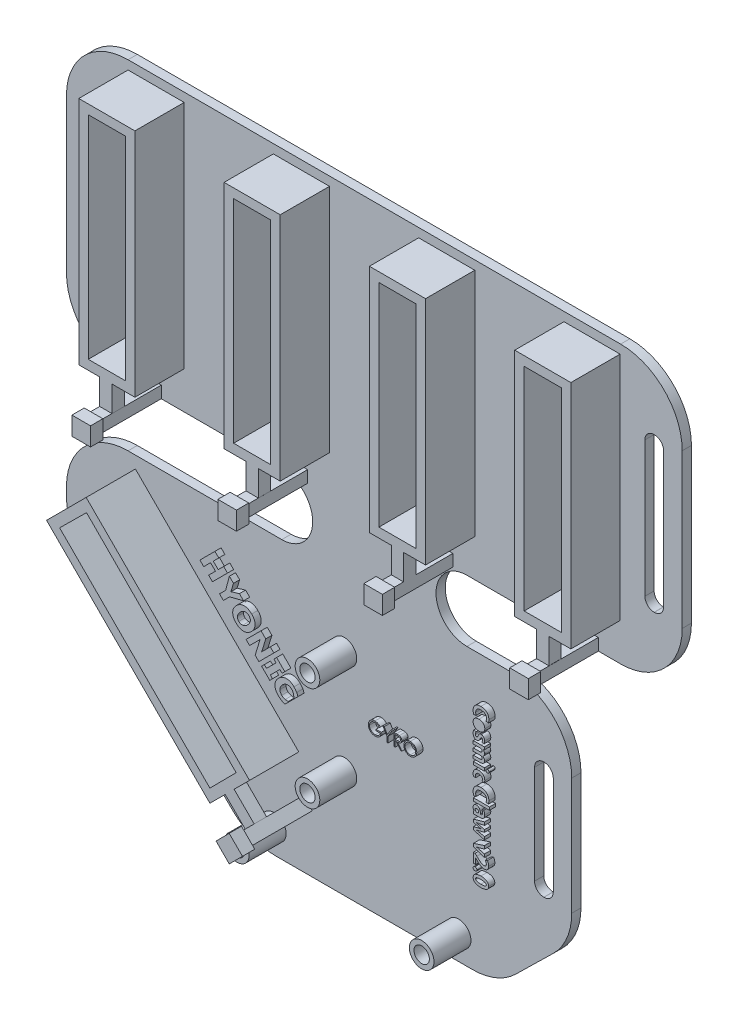
SolidWorks part; units mm, degrees
ref_plane "Front Plane" through (0, 0, 0) normal (0, 0, 1) x (1, 0, 0)
ref_plane "Top Plane" through (0, 0, 0) normal (0, 1, 0) x (1, 0, 0)
ref_plane "Right Plane" through (0, 0, 0) normal (1, 0, 0) x (0, 0, -1)
sketch "Sketch2" plane through (0, 0, 0) normal (0, 0, 1) x (1, 0, 0)
  line L1 (-56.1458, 50) -> (23.8542, 50)
  line L2 (-66.1458, 40) -> (-66.1458, 15.009)
  line L3 (-32.1008, -50) -> (-0.1909, -50)
  line L4 (33.8542, 40) -> (33.8542, 15.009)
  line L5 (-31.1727, 5.009) -> (-66.1458, 5.009) construction
  line L7 (-66.1458, -5.009) -> (-31.1727, -5.009) construction
  line L9 (33.8542, 5.009) -> (-1.119, 5.009) construction
  line L10 (-66.1458, -15.009) -> (-66.1458, -16.4538)
  line L11 (-56.1458, 5.009) -> (-31.1727, 5.009)
  line L13 (-56.1458, -5.009) -> (-31.1727, -5.009)
  line L15 (23.8542, 5.009) -> (-1.119, 5.009)
  line L17 (5.9119, -5.009) -> (-1.119, -5.009)
  line L19 (15.9119, -15.009) -> (15.9119, -34.0239)
  line L20 (-1.119, -5.009) -> (15.9119, -5.009) construction
  line L22 (-16.1458, -50) -> (3.89, -50) construction
  line L23 (-16.1458, -50) -> (-36.1817, -50) construction
  line L24 (-63.1424, -23.5986) -> (-39.0974, -47.1448)
  line L27 (6.8057, -47.1448) -> (12.9084, -41.1687)
  arc A0 (-31.1727, -5.009) -> (-31.1727, 5.009) centre (-31.1727, 0) ccw
  arc A1 (-1.119, 5.009) -> (-1.119, -5.009) centre (-1.119, 0) ccw
  arc A2 (-32.1008, -50) -> (-39.0974, -47.1448) centre (-32.1008, -40) cw
  arc A3 (6.8057, -47.1448) -> (-0.1909, -50) centre (-0.1909, -40) cw
  arc A6 (-66.1458, -15.009) -> (-56.1458, -5.009) centre (-56.1458, -15.009) cw
  arc A7 (-66.1458, -16.4538) -> (-63.1424, -23.5986) centre (-56.1458, -16.4538) ccw
  arc A8 (-56.1458, 5.009) -> (-66.1458, 15.009) centre (-56.1458, 15.009) cw
  arc A9 (23.8542, 50) -> (33.8542, 40) centre (23.8542, 40) cw
  arc A10 (-56.1458, 50) -> (-66.1458, 40) centre (-56.1458, 40) ccw
  arc A11 (23.8542, 5.009) -> (33.8542, 15.009) centre (23.8542, 15.009) ccw
  arc A12 (12.9084, -41.1687) -> (15.9119, -34.0239) centre (5.9119, -34.0239) ccw
  arc A13 (5.9119, -5.009) -> (15.9119, -15.009) centre (5.9119, -15.009) cw
  point P17 (0, 0)
  point P39 (33.8542, 50)
  point P42 (-66.1458, 50)
  dimension "D2" = 10
  dimension "D3" = 10
  dimension "D4" = 10
  dimension "D1" = 100
extrude "Boss-Extrude2" add sketch "Sketch2" against normal blind 1.5 contours A7 L10 A6 L13 A0 L11 A8 L2 A10 L1 A9 L4 A11 L15 A1 L17 A13 L19 A12 L27 A3 L3 A2 L24
sketch "Sketch3" plane through (0, 0, 0) normal (0, 0, 1) x (1, 0, 0)
  circle A0 centre (-21.0035, -15.6832) radius 2
  circle A1 centre (-21.0035, -32.5746) radius 2
  dimension "D1" = 4
  dimension "D2" = 4
extrude "Boss-Extrude7" add sketch "Sketch3" along normal blind 6
sketch "Sketch8" plane through (0, 0, 6) normal (0, 0, 1) x (1, 0, 0)
  circle A0 centre (-21.0035, -15.6832) radius 1.25
  circle A1 centre (-21.0035, -32.5746) radius 1.25
  dimension "D1" = 2.5
  dimension "D2" = 2.5
extrude "Cut-Extrude1" cut sketch "Sketch8" against normal blind 5
sketch "Sketch9" plane through (0, 0, 0) normal (0, 0, 1) x (1, 0, 0)
  line L0 (-32.4619, -46.0299) -> (-2.4559, -46.0299) construction
  circle A0 centre (-32.4619, -46.0299) radius 2
  circle A1 centre (-2.4559, -46.0299) radius 2
  dimension "D1" = 4
  dimension "D2" = 4
extrude "Boss-Extrude8" add sketch "Sketch9" along normal blind 6
sketch "Sketch10" plane through (0, 0, 6) normal (0, 0, 1) x (1, 0, 0)
  circle A0 centre (-32.4619, -46.0299) radius 1.25
  circle A1 centre (-2.4559, -46.0299) radius 1.25
  dimension "D1" = 2.5
  dimension "D2" = 2.5
extrude "Cut-Extrude2" cut sketch "Sketch10" against normal blind 5
sketch "Sketch11" plane through (0, 0, 0) normal (0, 0, 1) x (1, 0, 0)
  line L0 (-66.1458, 40) -> (-63.1043, 40) construction
  line L1 (-66.1458, 15.009) -> (-63.1043, 15.009) construction
  line L2 (-63.1424, -23.5986) -> (-61.0425, -21.4987) construction
  line L3 (-61.6043, 40) -> (-61.5553, 40)
  line L4 (-63.1043, 38.5) -> (-63.1043, 16.509)
  line L5 (-61.6043, 15.009) -> (-61.5553, 15.009)
  line L6 (-60.0553, 38.5) -> (-60.0553, 16.509)
  line L7 (-61.0425, -21.4987) -> (-43.3557, -39.1855) construction
  line L8 (-43.3557, -39.1855) -> (-45.4556, -41.2854) construction
  line L9 (-59.9818, -22.5594) -> (-44.4164, -38.1248)
  line L10 (-42.295, -38.1248) -> (-42.2889, -38.1187)
  line L11 (-42.2889, -35.9973) -> (-57.8543, -20.4319)
  line L12 (-59.9757, -20.4319) -> (-59.9818, -20.438)
  line L13 (15.9119, -15.009) -> (12.9157, -15.009) construction
  line L14 (12.9157, -15.009) -> (12.9157, -34.0239) construction
  line L15 (12.9157, -34.0239) -> (15.9119, -34.0239) construction
  line L16 (33.8542, 40) -> (30.8329, 40) construction
  line L17 (30.8329, 40) -> (30.8329, 15.009) construction
  line L18 (30.8329, 15.009) -> (33.8542, 15.009) construction
  line L20 (29.3329, 40) -> (29.2903, 40)
  line L21 (30.8329, 38.5) -> (30.8329, 16.509)
  line L22 (29.3329, 15.009) -> (29.2903, 15.009)
  line L23 (27.7903, 38.5) -> (27.7903, 16.509)
  line L24 (11.4157, -15.009) -> (11.3731, -15.009)
  line L25 (12.9157, -16.509) -> (12.9157, -32.5239)
  line L26 (11.4157, -34.0239) -> (11.3731, -34.0239)
  line L27 (9.8731, -16.509) -> (9.8731, -32.5239)
  arc A0 (29.2903, 40) -> (27.7903, 38.5) centre (29.2903, 38.5) ccw
  arc A1 (29.3329, 40) -> (30.8329, 38.5) centre (29.3329, 38.5) cw
  arc A2 (30.8329, 16.509) -> (29.3329, 15.009) centre (29.3329, 16.509) cw
  arc A3 (29.2903, 15.009) -> (27.7903, 16.509) centre (29.2903, 16.509) cw
  arc A4 (11.4157, -15.009) -> (12.9157, -16.509) centre (11.4157, -16.509) cw
  arc A5 (11.3731, -15.009) -> (9.8731, -16.509) centre (11.3731, -16.509) ccw
  arc A6 (12.9157, -32.5239) -> (11.4157, -34.0239) centre (11.4157, -32.5239) cw
  arc A7 (11.3731, -34.0239) -> (9.8731, -32.5239) centre (11.3731, -32.5239) cw
  arc A8 (-42.2889, -38.1187) -> (-42.2889, -35.9973) centre (-43.3495, -37.058) ccw
  arc A9 (-44.4164, -38.1248) -> (-42.295, -38.1248) centre (-43.3557, -37.0642) ccw
  arc A10 (-59.9818, -22.5594) -> (-59.9818, -20.438) centre (-58.9212, -21.4987) cw
  arc A11 (-57.8543, -20.4319) -> (-59.9757, -20.4319) centre (-58.915, -21.4925) ccw
  arc A12 (-61.5553, 15.009) -> (-60.0553, 16.509) centre (-61.5553, 16.509) ccw
  arc A13 (-61.6043, 15.009) -> (-63.1043, 16.509) centre (-61.6043, 16.509) cw
  arc A14 (-61.5553, 40) -> (-60.0553, 38.5) centre (-61.5553, 38.5) cw
  arc A15 (-63.1043, 38.5) -> (-61.6043, 40) centre (-61.6043, 38.5) cw
  dimension "D1" = 1.5
extrude "Cut-Extrude3" cut sketch "Sketch11" against normal up to surface (1.5 mm away) up to face at (-19.1362, -5.3071, -1.5)
sketch "Sketch12" plane through (0, 0, 0) normal (0, 0, 1) x (1, 0, 0)
  line L0 (-60.0553, 30.6424) -> (-56.1227, 30.6424) construction
  line L1 (-56.1458, 50) -> (-56.1458, 48.5494) construction
  line L2 (-32.5458, 48.5494) -> (-32.5458, 11.0834)
  line L3 (-56.1458, 48.5494) -> (-47.0304, 48.5494)
  line L4 (-56.1458, 48.5494) -> (-56.1458, 11.0834)
  line L5 (-56.1458, 11.0834) -> (-47.0304, 11.0834)
  line L6 (-47.0304, 48.5494) -> (-47.0304, 11.0834)
  line L7 (-32.5458, 48.5494) -> (-23.4304, 48.5494)
  line L8 (-23.4304, 48.5494) -> (-23.4304, 11.0834)
  line L9 (-32.5458, 11.0834) -> (-23.4304, 11.0834)
  line L10 (-8.9458, 48.5494) -> (-8.9458, 11.0834)
  line L11 (-8.9458, 48.5494) -> (0.1696, 48.5494)
  line L12 (0.1696, 48.5494) -> (0.1696, 11.0834)
  line L13 (-8.9458, 11.0834) -> (0.1696, 11.0834)
  line L14 (14.6542, 48.5494) -> (14.6542, 11.0834)
  line L15 (14.6542, 48.5494) -> (23.7696, 48.5494)
  line L16 (23.7696, 48.5494) -> (23.7696, 11.0834)
  line L17 (14.6542, 11.0834) -> (23.7696, 11.0834)
  line L18 (-56.1458, 48.5494) -> (-32.5458, 48.5494) construction
  line L19 (-61.3798, -13.3978) -> (-34.8496, -39.928)
  line L20 (-34.8496, -39.928) -> (-28.4161, -33.4944)
  line L21 (-28.4161, -33.4944) -> (-54.9463, -6.9642)
  line L22 (-54.9463, -6.9642) -> (-61.3798, -13.3978)
  dimension "D2" = 23.6
  dimension "D1" = 4
extrude "Boss-Extrude9" add sketch "Sketch12" along normal blind 8
sketch "Sketch13" plane through (0, 0, 8) normal (0, 0, 1) x (1, 0, 0)
  line L0 (-54.1669, 48.5494) -> (-54.1669, 47.0408) construction
  line L1 (-56.1458, 47.0408) -> (-54.6076, 47.0408) construction
  line L2 (-54.6076, 47.0408) -> (-54.6076, 48.5494) construction
  line L3 (-47.0304, 11.0834) -> (-47.0304, 12.632) construction
  line L4 (-47.0304, 12.632) -> (-48.5675, 12.632) construction
  line L5 (-48.5675, 12.632) -> (-48.5675, 11.0834) construction
  line L6 (-32.5458, 48.5494) -> (-30.9967, 48.5494) construction
  line L7 (-54.6076, 47.0408) -> (-48.5675, 47.0408)
  line L8 (-54.6076, 47.0408) -> (-54.6076, 12.632)
  line L9 (-54.6076, 12.632) -> (-48.5675, 12.632)
  line L10 (-48.5675, 47.0408) -> (-48.5675, 12.632)
  line L11 (-30.9967, 48.5494) -> (-30.9967, 47.0408) construction
  line L12 (-30.9967, 47.0408) -> (-32.5458, 47.0408) construction
  line L13 (-23.4304, 11.0834) -> (-23.4304, 12.632) construction
  line L14 (-23.4304, 12.632) -> (-24.9724, 12.632) construction
  line L15 (-24.9724, 12.632) -> (-24.9724, 11.0834) construction
  line L16 (-8.9458, 11.0834) -> (-8.9458, 12.632) construction
  line L17 (-8.9458, 12.632) -> (-7.4016, 12.632) construction
  line L18 (-7.4016, 12.632) -> (-7.4016, 11.0834) construction
  line L19 (-7.4016, 11.0834) -> (0.1696, 11.0834) construction
  line L20 (0.1696, 11.0834) -> (0.1696, 12.632) construction
  line L21 (0.1696, 12.632) -> (-1.3773, 12.632) construction
  line L22 (-1.3773, 12.632) -> (-1.3773, 11.0834) construction
  line L23 (-8.9458, 48.5494) -> (-7.4016, 48.5494) construction
  line L24 (-7.4016, 48.5494) -> (-7.4016, 47.0408) construction
  line L25 (-7.4016, 47.0408) -> (-8.9458, 47.0408) construction
  line L26 (14.6542, 48.5494) -> (16.1861, 48.5494) construction
  line L27 (16.1861, 48.5494) -> (16.1861, 47.0408) construction
  line L28 (16.1861, 47.0408) -> (14.6542, 47.0408) construction
  line L29 (23.7696, 11.0834) -> (23.7696, 12.632) construction
  line L30 (23.7696, 12.632) -> (22.2818, 12.632) construction
  line L31 (22.2818, 12.632) -> (22.2818, 11.0834) construction
  line L32 (-61.3798, -13.3978) -> (-60.3186, -12.3365) construction
  line L33 (-30.9967, 47.0408) -> (-24.9724, 47.0408)
  line L34 (-30.9967, 47.0408) -> (-30.9967, 12.632)
  line L35 (-30.9967, 12.632) -> (-24.9724, 12.632)
  line L36 (-24.9724, 47.0408) -> (-24.9724, 12.632)
  line L37 (-1.3773, 12.632) -> (-7.4016, 12.632)
  line L38 (-1.3773, 12.632) -> (-1.3773, 47.0408)
  line L39 (-1.3773, 47.0408) -> (-7.4016, 47.0408)
  line L40 (-7.4016, 12.632) -> (-7.4016, 47.0408)
  line L41 (16.1861, 47.0408) -> (22.2818, 47.0408)
  line L42 (16.1861, 47.0408) -> (16.1861, 12.632)
  line L43 (16.1861, 12.632) -> (22.2818, 12.632)
  line L44 (22.2818, 47.0408) -> (22.2818, 12.632)
  line L45 (-54.9463, -6.9642) -> (-61.3798, -13.3978) construction
  line L46 (-60.3186, -12.3365) -> (-59.2574, -13.3978) construction
  line L47 (-59.2574, -13.3978) -> (-60.3186, -14.459) construction
  line L48 (-61.3798, -13.3978) -> (-34.8496, -39.928) construction
  line L49 (-60.3186, -14.459) -> (-34.8496, -39.928) construction
  line L50 (-34.8496, -39.928) -> (-28.4161, -33.4944) construction
  line L51 (-28.4161, -33.4944) -> (-29.5014, -32.4091) construction
  line L52 (-28.4161, -33.4944) -> (-54.9463, -6.9642) construction
  line L53 (-29.5014, -32.4091) -> (-30.5893, -33.497) construction
  line L54 (-30.5893, -33.497) -> (-29.5039, -34.5823) construction
  line L55 (-54.9463, -6.9642) -> (-55.9749, -7.9928) construction
  line L56 (-55.9749, -7.9928) -> (-54.8908, -9.0769) construction
  line L57 (-54.8908, -9.0769) -> (-53.8622, -8.0483) construction
  line L58 (-34.8496, -39.928) -> (-35.9138, -38.8638) construction
  line L59 (-35.9138, -38.8638) -> (-34.8496, -37.7996) construction
  line L60 (-34.8496, -37.7996) -> (-33.7854, -38.8638) construction
  line L61 (-30.5893, -33.497) -> (-34.8496, -37.7996)
  line L62 (-34.8496, -37.7996) -> (-59.2574, -13.3978)
  line L63 (-59.2574, -13.3978) -> (-54.8908, -9.0769)
  line L64 (-54.8908, -9.0769) -> (-30.5893, -33.497)
extrude "Cut-Extrude4" cut sketch "Sketch13" against normal blind 7
sketch "Sketch14" plane through (0, 0, 0) normal (0, 0, 1) x (1, 0, 0)
  line L0 (-56.1458, 11.0834) -> (-47.0304, 5.009) construction
  line L1 (-56.1458, 5.009) -> (-31.1727, 5.009) construction
  line L2 (-47.0304, 5.009) -> (-47.0304, 11.0834) construction
  line L3 (-47.0304, 11.0834) -> (-56.1458, 5.009) construction
  line L4 (-50.4257, 6.9592) -> (-27.9881, 6.9303) construction
  line L13 (-28.9979, 6.9303) -> (-26.9783, 5.009) construction
  line L14 (-28.9979, 5.009) -> (-26.9783, 6.9303) construction
  line L15 (23.8542, 5.009) -> (-1.119, 5.009) construction
  line L16 (-52.7505, 6.9303) -> (-50.7505, 6.9303)
  line L17 (-52.7505, 6.9303) -> (-52.7505, 5.009)
  line L18 (-52.7505, 5.009) -> (-50.7505, 5.009)
  line L19 (-50.7505, 6.9303) -> (-50.7505, 5.009)
  line L20 (-52.7505, 6.9303) -> (-50.7505, 5.009) construction
  line L21 (-52.7505, 5.009) -> (-50.7505, 6.9303) construction
  line L22 (-28.9979, 6.9303) -> (-26.9783, 6.9303)
  line L23 (-28.9979, 6.9303) -> (-28.9979, 5.009)
  line L24 (-28.9979, 5.009) -> (-26.9783, 5.009)
  line L25 (-26.9783, 6.9303) -> (-26.9783, 5.009)
  line L26 (-28.9979, 6.9303) -> (-26.9783, 5.009) construction
  line L27 (-28.9979, 5.009) -> (-26.9783, 6.9303) construction
  line L28 (-5.3797, 6.9303) -> (-3.3965, 6.9303)
  line L29 (-5.3797, 6.9303) -> (-5.3797, 5.009)
  line L30 (-5.3797, 5.009) -> (-3.3965, 5.009)
  line L31 (-3.3965, 6.9303) -> (-3.3965, 5.009)
  line L32 (-5.3797, 6.9303) -> (-3.3965, 5.009) construction
  line L33 (-5.3797, 5.009) -> (-3.3965, 6.9303) construction
  line L34 (18.1897, 6.9303) -> (20.2341, 6.9303)
  line L35 (18.1897, 6.9303) -> (18.1897, 5.009)
  line L36 (18.1897, 5.009) -> (20.2341, 5.009)
  line L37 (20.2341, 6.9303) -> (20.2341, 5.009)
  line L38 (18.1897, 6.9303) -> (20.2341, 5.009) construction
  line L39 (18.1897, 5.009) -> (20.2341, 6.9303) construction
  point P5 (-51.7505, 5.9696)
  point P13 (-27.9881, 5.9696)
  point P21 (-27.9881, 5.9696)
  point P22 (-4.3881, 5.9696)
  point P27 (19.2119, 5.9696)
  dimension "D1" = 1.9214
  dimension "D2" = 2
extrude "Boss-Extrude10" add sketch "Sketch14" along normal blind 12
sketch "Sketch16" plane through (0, 6.9303, 0) normal (0, 1, 0) x (1, 0, 0)
  line L0 (23.7696, -8) -> (14.6542, -8) construction
  line L1 (18.1897, -8) -> (20.209, -8)
  line L2 (18.1897, -8) -> (18.1897, -6)
  line L3 (18.1897, -6) -> (20.209, -6)
  line L4 (20.209, -8) -> (20.209, -6)
  line L5 (18.1897, -12) -> (18.1897, 0) construction
  line L6 (0.1696, -8) -> (-8.9458, -8) construction
  line L7 (-5.3797, -8) -> (-3.3965, -8)
  line L8 (-5.3797, -8) -> (-5.3797, -6)
  line L9 (-5.3797, -6) -> (-3.3965, -6)
  line L10 (-3.3965, -8) -> (-3.3965, -6)
  line L11 (-5.3797, -12) -> (-5.3797, 0) construction
  line L12 (-3.3965, -12) -> (-3.3965, 0) construction
  line L13 (-23.4304, -8) -> (-32.5458, -8) construction
  line L14 (-28.9979, -8) -> (-26.9792, -8)
  line L15 (-28.9979, -8) -> (-28.9979, -6)
  line L16 (-28.9979, -6) -> (-26.9792, -6)
  line L17 (-26.9792, -8) -> (-26.9792, -6)
  line L18 (-28.9979, -12) -> (-28.9979, 0) construction
  line L19 (-47.0304, -8) -> (-56.1458, -8) construction
  line L20 (-52.7505, -8) -> (-50.7478, -8)
  line L21 (-52.7505, -8) -> (-52.7505, -6)
  line L22 (-52.7505, -6) -> (-50.7478, -6)
  line L23 (-50.7478, -8) -> (-50.7478, -6)
  line L24 (-52.7505, -12) -> (-52.7505, 0) construction
extrude "Boss-Extrude11" add sketch "Sketch16" along normal up to surface (4.153 mm away) up to face at (-51.5881, 11.0834, 4)
sketch "Sketch17" plane through (0, 0, 0) normal (0, 0, 1) x (1, 0, 0)
  line L0 (-28.3797, -39.9643) -> (-29.1078, -40.6924) construction
  line L1 (-29.1078, -40.6924) -> (-27.6714, -39.256) construction
  line L2 (-29.1078, -40.6924) -> (-27.6714, -39.256)
  line L3 (-27.6714, -39.256) -> (-26.235, -40.6924)
  line L4 (-26.235, -40.6924) -> (-27.6714, -42.1287)
  line L5 (-27.6714, -42.1287) -> (-29.1078, -40.6924)
extrude "Boss-Extrude12" add sketch "Sketch17" along normal blind 12
sketch "Sketch18" plane through (5.7923, -5.7923, 0) normal (-0.7071, 0.7071, 0) x (0, 0, 1)
  line L0 (8, -43.7773) -> (8, -52.8757) construction
  line L1 (8, -47.3132) -> (5.986, -47.3132)
  line L2 (8, -47.3132) -> (8, -49.3668)
  line L3 (8, -49.3668) -> (5.986, -49.3668)
  line L4 (5.986, -47.3132) -> (5.986, -49.3668)
extrude "Boss-Extrude13" add sketch "Sketch18" along normal up to surface (4.6006 mm away) up to face at (-31.6328, -36.7112, 4)
sketch "Sketch19" plane through (0, 0, 0) normal (0, 0, 1) x (1, 0, 0)
  text T0 "Cosmic Claw v2.0" font "@Adobe Gothic Std B" height 2.5
extrude "Boss-Extrude14" add sketch "Sketch19" along normal blind 1
sketch "Sketch20" plane through (0, 0, 0) normal (0, 0, 1) x (1, 0, 0)
  text T0 "HYONIC" font "Tahoma" height 3.5
  point P2 (-43.7372, -13.2651)
  point P4 (-29.8089, -27.0608)
extrude "Boss-Extrude15" add sketch "Sketch20" along normal blind 1
sketch "Sketch21" plane through (0, 0, 0) normal (0, 0, 1) x (1, 0, 0)
  line L0 (-16.2785, -24.0098) -> (-8.1868, -24.0098) construction
  text T0 "GYRO" font "Century Gothic" height 2
extrude "Boss-Extrude16" add sketch "Sketch21" along normal blind 1
sketch "Sketch22" plane through (0, 0, 12) normal (0, 0, 1) x (1, 0, 0)
  line L0 (-52.7505, 6.9303) -> (-50.7505, 5.009) construction
  line L1 (-50.7505, 5.009) -> (-50.7505, 6.9303) construction
  line L2 (-50.7505, 6.9303) -> (-52.7505, 5.009) construction
  line L3 (-29.5634, 7.4604) -> (-26.5376, 4.4789) construction
  line L4 (-53.2634, 7.4604) -> (-50.2376, 7.4604)
  line L5 (-53.2634, 7.4604) -> (-53.2634, 4.4789)
  line L6 (-53.2634, 4.4789) -> (-50.2376, 4.4789)
  line L7 (-50.2376, 7.4604) -> (-50.2376, 4.4789)
  line L8 (-53.2634, 7.4604) -> (-50.2376, 4.4789) construction
  line L9 (-53.2634, 4.4789) -> (-50.2376, 7.4604) construction
  line L10 (-29.5634, 4.4789) -> (-26.5376, 7.4604) construction
  line L11 (-29.5634, 7.4604) -> (-29.5634, 4.4789)
  line L12 (-29.5634, 7.4604) -> (-26.5376, 7.4604)
  line L13 (-26.5376, 7.4604) -> (-26.5376, 4.4789)
  line L14 (-29.5634, 4.4789) -> (-26.5376, 4.4789)
  line L15 (-5.8634, 7.4604) -> (-2.8376, 4.4789) construction
  line L16 (-5.8634, 4.4789) -> (-2.8376, 7.4604) construction
  line L17 (-5.8634, 7.4604) -> (-5.8634, 4.4789)
  line L18 (-5.8634, 7.4604) -> (-2.8376, 7.4604)
  line L19 (-2.8376, 7.4604) -> (-2.8376, 4.4789)
  line L20 (-5.8634, 4.4789) -> (-2.8376, 4.4789)
  line L21 (17.8366, 7.4604) -> (20.8624, 4.4789) construction
  line L22 (17.8366, 4.4789) -> (20.8624, 7.4604) construction
  line L23 (17.8366, 7.4604) -> (17.8366, 4.4789)
  line L24 (17.8366, 7.4604) -> (20.8624, 7.4604)
  line L25 (20.8624, 7.4604) -> (20.8624, 4.4789)
  line L26 (17.8366, 4.4789) -> (20.8624, 4.4789)
  line L27 (-51.7505, 5.9696) -> (-28.0505, 5.9696) construction
  point P4 (-51.7505, 5.9696)
  point P14 (-28.0505, 5.9696)
  point P19 (-4.3505, 5.9696)
  point P24 (19.3495, 5.9696)
  dimension "D2" = 23.7
  dimension "D1" = 4
extrude "Boss-Extrude17" add sketch "Sketch22" against normal blind 2
sketch "Sketch23" plane through (0, 0, 12) normal (0, 0, 1) x (1, 0, 0)
  line L0 (-27.7216, -40.6784) -> (-28.7631, -39.6369) construction
  line L1 (-28.7631, -39.6369) -> (-27.7216, -38.5954) construction
  line L2 (-27.7216, -38.5954) -> (-25.5658, -40.7511)
  line L3 (-25.5658, -40.7511) -> (-27.7049, -42.8902)
  line L4 (-27.7049, -42.8902) -> (-29.844, -40.7511)
  line L5 (-27.7216, -38.5954) -> (-29.844, -40.7511)
extrude "Boss-Extrude18" add sketch "Sketch23" against normal blind 2
